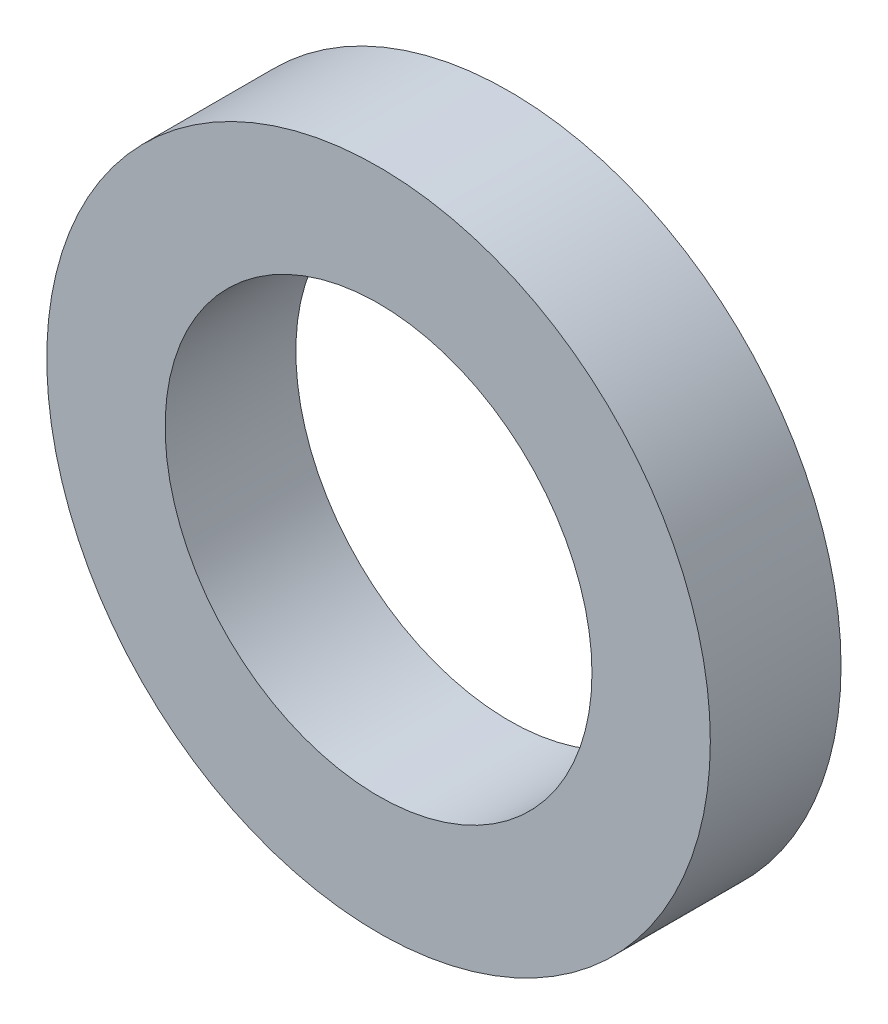
SolidWorks part; units mm, degrees
material "Plain Carbon Steel"
ref_plane "Front Plane" through (0, 0, 0) normal (0, 0, 1) x (1, 0, 0)
ref_plane "Top Plane" through (0, 0, 0) normal (0, 1, 0) x (1, 0, 0)
ref_plane "Right Plane" through (0, 0, 0) normal (1, 0, 0) x (0, 0, -1)
sketch "Sketch1" plane through (0, 0, 0) normal (0, 0, 1) x (1, 0, 0)
  circle A2 centre (164.7998, 1350.514) radius 22.8092
  circle A3 centre (164.7998, 1350.514) radius 22.8092
  circle A5 centre (164.7998, 1350.514) radius 35.4584
  circle A6 centre (164.7998, 1350.514) radius 35.4584
  dimension "D1" = 0.0508
  dimension "D2" = 12.7
extrude "Boss-Extrude1" add sketch "Sketch1" along normal blind 13.97
